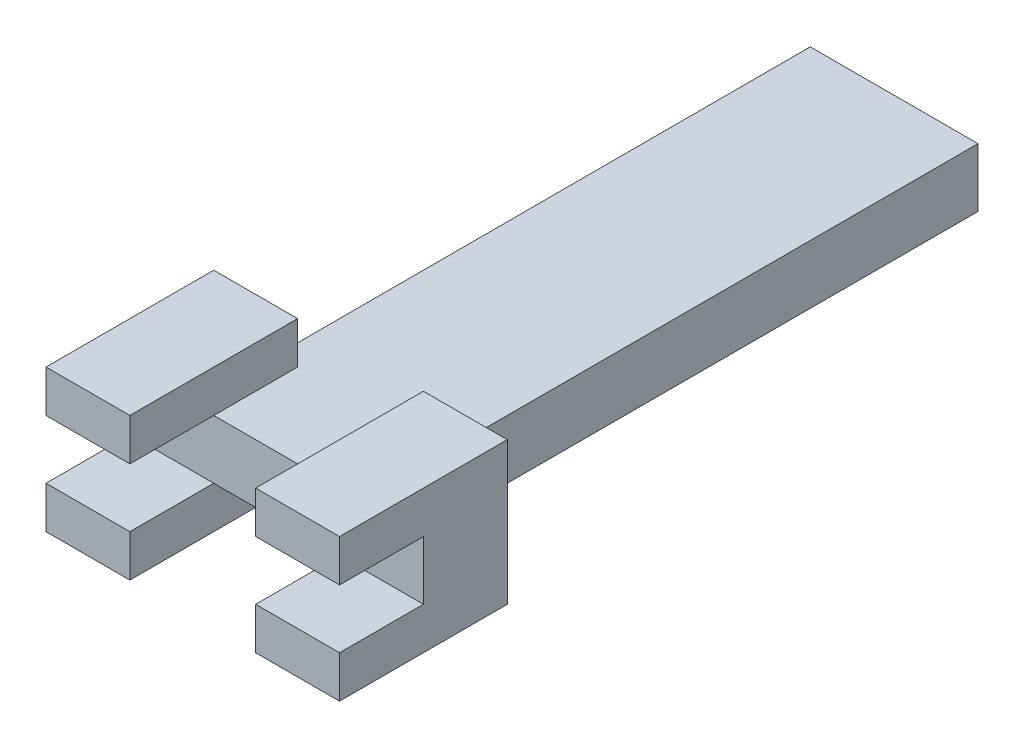
SolidWorks part; units mm, degrees
ref_plane "Front Plane" through (0, 0, 0) normal (0, 0, 1) x (1, 0, 0)
ref_plane "Top Plane" through (0, 0, 0) normal (0, 1, 0) x (1, 0, 0)
ref_plane "Right Plane" through (0, 0, 0) normal (1, 0, 0) x (0, 0, -1)
sketch "Sketch1" plane through (0, 0, 0) normal (0, 1, 0) x (1, 0, 0)
  line L1 (0, 0) -> (20, 0)
  line L2 (0, 0) -> (0, 73.6255)
  line L3 (0, 73.6255) -> (20, 73.6255)
  line L4 (20, 0) -> (20, 73.6255)
  dimension "D1" = 73.6255
  dimension "D2" = 20
extrude "Boss-Extrude1" add sketch "Sketch1" along normal blind 7
sketch "Sketch2" plane through (0, 7, 0) normal (0, 1, 0) x (1, 0, 0)
  line L0 (0, 0) -> (20, 0) construction
  line L1 (2.5, 10) -> (17.5, 10) construction
  line L2 (2.5, 10) -> (2.5, 0) construction
  line L3 (2.5, 0) -> (17.5, 0) construction
  line L4 (17.5, 10) -> (17.5, 0) construction
  line L14 (2.5, 0) -> (-7.5, 0)
  line L15 (2.5, 0) -> (2.5, 10)
  line L16 (2.5, 10) -> (-7.5, 10)
  line L17 (-7.5, 0) -> (-7.5, 10)
  line L18 (17.5, 0) -> (27.5, 0)
  line L19 (17.5, 0) -> (17.5, 10)
  line L20 (17.5, 10) -> (27.5, 10)
  line L21 (27.5, 0) -> (27.5, 10)
  point P4 (10, 0)
  point P7 (10, 0)
  dimension "D1" = 10
  dimension "D2" = 15
  dimension "D3" = 10
  dimension "D4" = 10
extrude "Boss-Extrude2" add sketch "Sketch2" along normal blind 5
sketch "Sketch3" plane through (0, 0, 0) normal (0, 0, 1) x (1, 0, 0)
  line L1 (-7.5, 12) -> (2.5, 12)
  line L2 (-7.5, 12) -> (-7.5, 7)
  line L3 (-7.5, 7) -> (2.5, 7)
  line L4 (2.5, 12) -> (2.5, 7)
  line L5 (17.5, 12) -> (27.5, 12)
  line L6 (17.5, 12) -> (17.5, 7)
  line L7 (17.5, 7) -> (27.5, 7)
  line L8 (27.5, 12) -> (27.5, 7)
extrude "Boss-Extrude3" add sketch "Sketch3" along normal blind 10
sketch "Sketch4" plane through (0, 7, 0) normal (0, -1, 0) x (1, 0, 0)
  line L1 (0, 0) -> (-7.5, 0)
  line L2 (0, 0) -> (0, -10)
  line L3 (0, -10) -> (-7.5, -10)
  line L4 (-7.5, 0) -> (-7.5, -10)
  line L5 (20, 0) -> (27.5, 0)
  line L6 (20, 0) -> (20, -10)
  line L7 (20, -10) -> (27.5, -10)
  line L8 (27.5, 0) -> (27.5, -10)
extrude "Boss-Extrude4" add sketch "Sketch4" along normal blind 3.5
ref_plane "Plane1" through (0, 3.5, 0) normal (0, 1, 0) x (1, 0, 0)
mirror "Mirror1" about plane through (0, 3.5, 0) normal (0, 1, 0) of "Boss-Extrude4", "Boss-Extrude3", "Boss-Extrude2"
